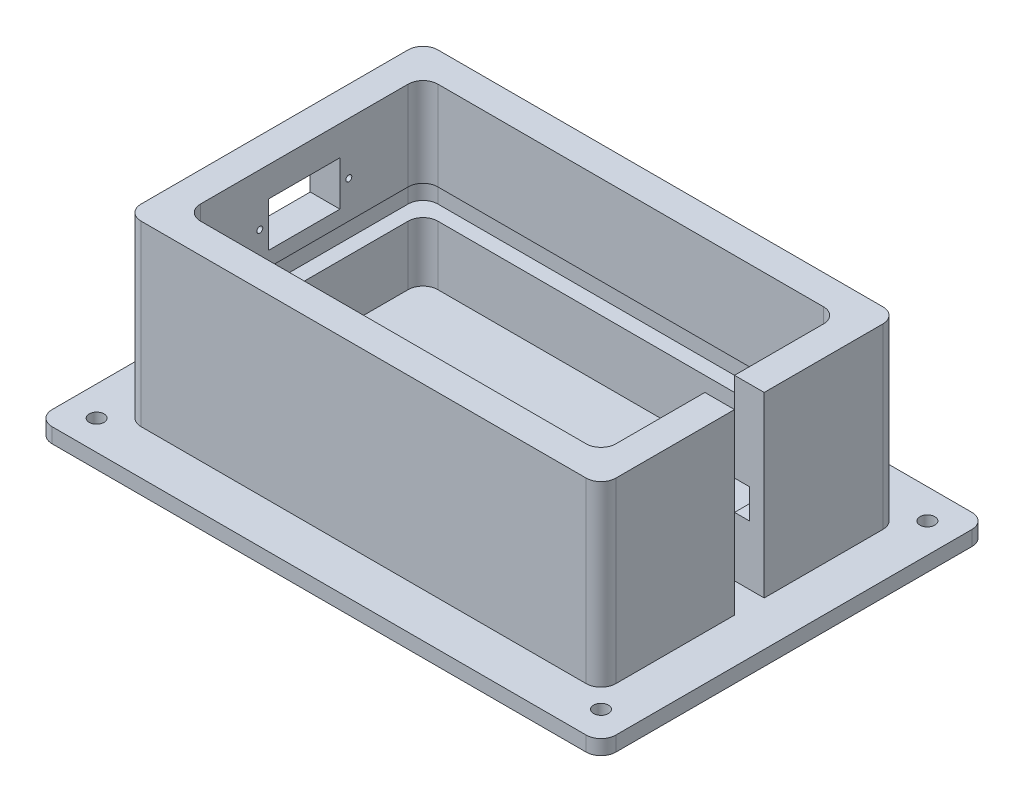
SolidWorks part; units mm, degrees
ref_plane "前基準面" through (0, 0, 0) normal (0, 0, 1) x (1, 0, 0)
ref_plane "上基準面" through (0, 0, 0) normal (0, 1, 0) x (1, 0, 0)
ref_plane "右基準面" through (0, 0, 0) normal (1, 0, 0) x (0, 0, -1)
sketch "草圖1" plane through (0, 0, 0) normal (0, 1, 0) x (1, 0, 0)
  line L0 (-85, 55) -> (-85, -55) construction
  line L5 (-85, -55) -> (85, -55) construction
  line L6 (85, -55) -> (85, 55) construction
  line L7 (85, 55) -> (-85, 55) construction
  line L9 (-95, 65) -> (95, 65)
  line L10 (-95, 65) -> (-95, -65)
  line L11 (-95, -65) -> (95, -65)
  line L12 (95, 65) -> (95, -65)
  line L13 (-95, 65) -> (95, -65) construction
  line L14 (-95, -65) -> (95, 65) construction
  circle A0 centre (-85, 55) radius 2.5
  circle A1 centre (85, 55) radius 2.5
  circle A2 centre (-85, -55) radius 2.5
  circle A3 centre (85, -55) radius 2.5
  point P0 (0, 0)
  point P10 (0, 0)
  dimension "D3" = 10
  dimension "D1" = 170
  dimension "D2" = 110
  dimension "D4" = 10
  dimension "D5" = 10
  dimension "D6" = 10
extrude "填料-伸長1" add sketch "草圖1" along normal blind 5
sketch "草圖2" plane through (0, 5, 0) normal (0, 1, 0) x (1, 0, 0)
  line L7 (-95, 65) -> (-95, -65) construction
  line L8 (95, 65) -> (-95, 65) construction
  line L10 (-80, 45) -> (-80, -45)
  line L11 (75, -50) -> (-75, -50)
  line L12 (80, 45) -> (80, 5)
  line L13 (75, 50) -> (-75, 50)
  line L18 (95, -65) -> (95, 65) construction
  line L19 (-95, -65) -> (95, -65) construction
  line L24 (65, 40) -> (-65, 40)
  line L25 (-70, 35) -> (-70, -35)
  line L26 (65, -40) -> (-65, -40)
  line L27 (70, 35) -> (70, 5)
  line L28 (80, -50) -> (-80, -50) construction
  line L29 (80, 50) -> (80, -50) construction
  line L30 (70, -40) -> (-70, -40) construction
  line L31 (70, 40) -> (70, -40) construction
  line L32 (-70, 40) -> (-70, -40) construction
  line L33 (-80, 50) -> (-80, -50) construction
  line L34 (70, 40) -> (-70, 40) construction
  line L35 (80, 50) -> (-80, 50) construction
  line L37 (70, -5) -> (80, -5)
  line L38 (70, 5) -> (80, 5)
  line L39 (70, -5) -> (70, -35)
  line L40 (80, -5) -> (80, -45)
  arc A0 (75, -50) -> (80, -45) centre (75, -45) ccw
  arc A1 (65, -40) -> (70, -35) centre (65, -35) ccw
  arc A2 (-70, -35) -> (-65, -40) centre (-65, -35) ccw
  arc A3 (-80, -45) -> (-75, -50) centre (-75, -45) ccw
  arc A4 (-65, 40) -> (-70, 35) centre (-65, 35) ccw
  arc A5 (-80, 45) -> (-75, 50) centre (-75, 45) cw
  arc A6 (80, 45) -> (75, 50) centre (75, 45) ccw
  arc A7 (65, 40) -> (70, 35) centre (65, 35) cw
  dimension "D6" = 5
  dimension "D7" = 5
  dimension "D1" = 15
  dimension "D2" = 15
  dimension "D3" = 15
  dimension "D4" = 15
  dimension "D5" = 10
  dimension "D8" = 10
  dimension "D9" = 35
  dimension "D10" = 35
  dimension "D11" = 100
  dimension "D12" = 80
  dimension "D13" = 140
fillet "圓角1" radius 5 4 edges at (-95, 2.5, 65) (95, 2.5, 65) (95, 2.5, -65) (-95, 2.5, -65)
extrude "填料-伸長2" add sketch "草圖2" along normal blind 60
sketch "草圖3" plane through (-80, 0, 0) normal (-1, 0, 0) x (0, 0, 1)
  line L0 (0, 30) -> (0, 47.5) construction
  line L1 (-60, 5) -> (60, 5) construction
  line L2 (-45, 5) -> (45, 5) construction
  line L3 (0, 47.5) -> (15, 47.5) construction
  line L4 (0, 5) -> (0, 30) construction
  line L6 (-12, 55) -> (12, 55)
  line L7 (-12, 55) -> (-12, 40)
  line L8 (-12, 40) -> (12, 40)
  line L9 (12, 55) -> (12, 40)
  line L10 (-12, 55) -> (12, 40) construction
  line L11 (-12, 40) -> (12, 55) construction
  circle A0 centre (15, 47.5) radius 1
  circle A1 centre (-15, 47.5) radius 1
  dimension "D4" = 15
  dimension "D5" = 2
  dimension "D1" = 24
  dimension "D2" = 35
  dimension "D3" = 15
extrude "除料-伸長1" cut sketch "草圖3" against normal blind 10
ref_plane "平面1" through (0, 30, 0) normal (0, 1, 0) x (1, 0, 0)
sketch "草圖4" plane through (0, 30, 0) normal (0, 1, 0) x (1, 0, 0)
  line L0 (75, 50) -> (-75, 50) construction
  line L1 (-70, 45) -> (70, 45)
  line L2 (-75, 40) -> (-75, -40)
  line L3 (-70, -45) -> (70, -45)
  line L4 (75, 40) -> (75, -40)
  line L5 (-75, 45) -> (75, -45) construction
  line L6 (-75, -45) -> (75, 45) construction
  line L7 (-80, 45) -> (-80, -45) construction
  line L9 (-65, 40) -> (65, 40)
  line L10 (-70, 35) -> (-70, -35)
  line L11 (-65, -40) -> (65, -40)
  line L12 (70, 35) -> (70, -35)
  line L13 (-70, 40) -> (70, -40) construction
  line L14 (-70, -40) -> (70, 40) construction
  arc A0 (70, -45) -> (75, -40) centre (70, -40) ccw
  arc A1 (-75, -40) -> (-70, -45) centre (-70, -40) ccw
  arc A2 (70, 45) -> (75, 40) centre (70, 40) cw
  arc A3 (-70, 45) -> (-75, 40) centre (-70, 40) ccw
  arc A4 (65, -40) -> (70, -35) centre (65, -35) ccw
  arc A5 (-70, -35) -> (-65, -40) centre (-65, -35) ccw
  arc A6 (-65, 40) -> (-70, 35) centre (-65, 35) ccw
  arc A7 (65, 40) -> (70, 35) centre (65, 35) cw
  point P0 (0, 0)
  point P22 (0, 0)
  dimension "D3" = 5
  dimension "D4" = 5
  dimension "D1" = 5
  dimension "D2" = 5
extrude "除料-伸長2" cut sketch "草圖4" against normal mid plane 10
